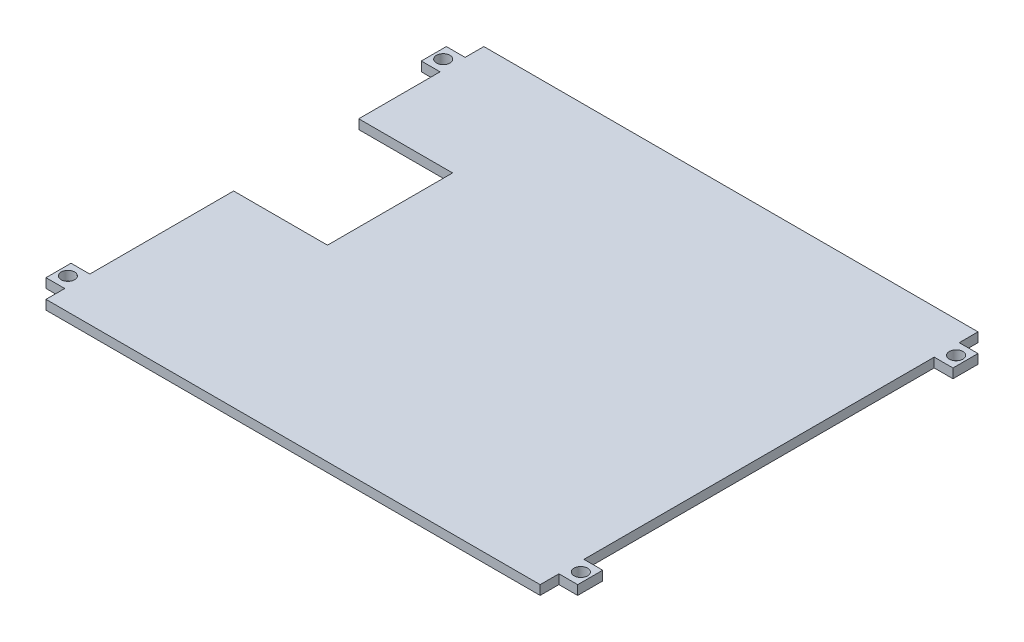
SolidWorks part; units mm, degrees
ref_plane "Front Plane" through (0, 0, 0) normal (0, 0, 1) x (1, 0, 0)
ref_plane "Top Plane" through (0, 0, 0) normal (0, 1, 0) x (1, 0, 0)
ref_plane "Right Plane" through (0, 0, 0) normal (1, 0, 0) x (0, 0, -1)
sketch "Sketch2" plane through (0, 0, 0) normal (0, 1, 0) x (1, 0, 0)
  line L0 (0, 0) -> (79, 0)
  line L1 (79, 0) -> (79, 70)
  line L2 (79, 70) -> (0, 70)
  line L3 (0, 70) -> (0, 50)
  line L4 (0, 50) -> (15, 50)
  line L5 (15, 50) -> (15, 30)
  line L6 (15, 30) -> (0, 30)
  line L7 (0, 30) -> (0, 0)
  dimension "D1" = 79
  dimension "D2" = 70
  dimension "D3" = 20
  dimension "D4" = 20
  dimension "D5" = 15
extrude "Boss-Extrude1" add sketch "Sketch2" along normal blind 1.5
sketch "Sketch3" plane through (79, 0, 0) normal (1, 0, 0) x (0, 0, -1)
  line L0 (0, 1.5) -> (70, 1.5) construction
  line L1 (3, 1.5) -> (7, 1.5)
  line L2 (3, 1.5) -> (3, 0)
  line L3 (3, 0) -> (7, 0)
  line L4 (7, 1.5) -> (7, 0)
  line L5 (0, 0) -> (70, 0) construction
  line L6 (0, 1.5) -> (0, 0) construction
  dimension "D1" = 4
  dimension "D2" = 3
extrude "Boss-Extrude2" add sketch "Sketch3" along normal blind 3
sketch "Sketch4" plane through (0, 1.5, 0) normal (0, 1, 0) x (1, 0, 0)
  line L0 (82, 7) -> (82, 3) construction
  line L1 (82, 7) -> (79, 7) construction
  circle A0 centre (80.5, 5) radius 1.08
  dimension "D3" = 2.16
  dimension "D1" = 1.5
  dimension "D2" = 2
extrude "Cut-Extrude1" cut sketch "Sketch4" against normal through all
pattern_linear "LPattern1" count 2 spacing 60 along (0, 0, -1) count 2 spacing 82 along (-1, 0, 0) of "Boss-Extrude2"
pattern_linear "LPattern2" count 2 spacing 60 along (0, 0, -1) count 2 spacing 82 along (-1, 0, 0) of "Cut-Extrude1"
